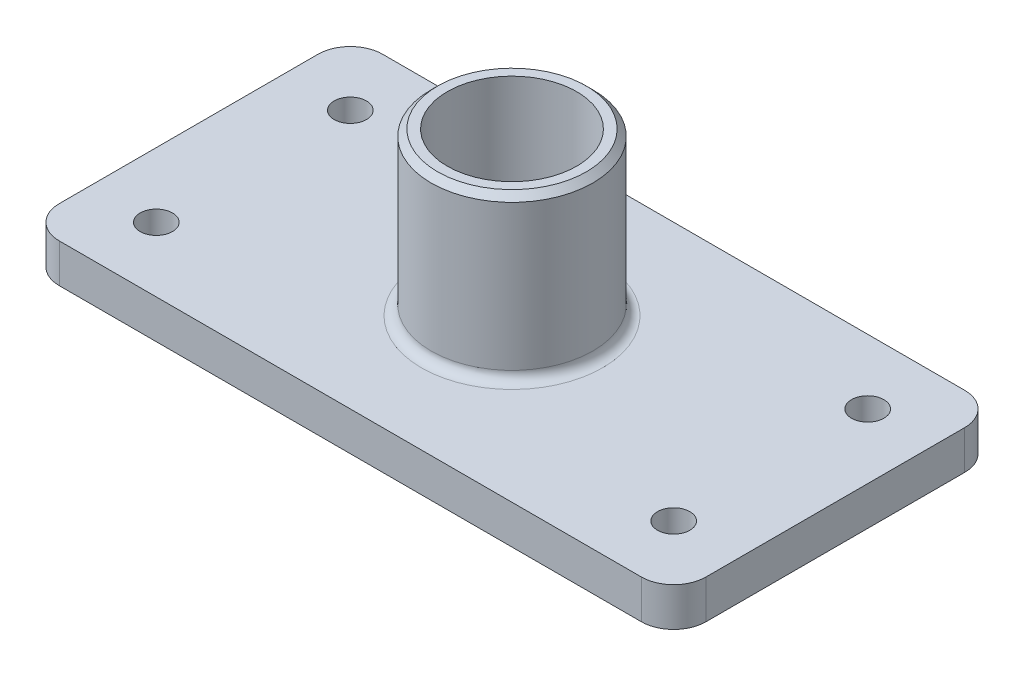
SolidWorks part; units mm, degrees
ref_plane "Front Plane" through (0, 0, 0) normal (0, 0, 1) x (1, 0, 0)
ref_plane "Top Plane" through (0, 0, 0) normal (0, 1, 0) x (1, 0, 0)
ref_plane "Right Plane" through (0, 0, 0) normal (1, 0, 0) x (0, 0, -1)
sketch "Sketch1" plane through (0, 0, 0) normal (0, 1, 0) x (1, 0, 0)
  line L1 (-90, -50) -> (90, -50)
  line L2 (-100, -40) -> (-100, 40)
  line L3 (-90, 50) -> (90, 50)
  line L4 (100, -40) -> (100, 40)
  line L5 (-100, -50) -> (100, 50) construction
  line L6 (-100, 50) -> (100, -50) construction
  arc A0 (90, -50) -> (100, -40) centre (90, -40) ccw
  arc A1 (90, 50) -> (100, 40) centre (90, 40) cw
  arc A2 (-100, 40) -> (-90, 50) centre (-90, 40) cw
  arc A3 (-90, -50) -> (-100, -40) centre (-90, -40) cw
  circle A4 centre (-80, -30) radius 5
  circle A5 centre (-80, 30) radius 5
  circle A6 centre (80, 30) radius 5
  circle A7 centre (80, -30) radius 5
  point P0 (0, 0)
  dimension "D3" = 10
  dimension "D4" = 10
  dimension "D1" = 100
  dimension "D2" = 200
  dimension "D5" = 20
  dimension "D6" = 60
  dimension "D7" = 20
  dimension "D8" = 160
extrude "Boss-Extrude1" add sketch "Sketch1" along normal blind 12
sketch "Sketch2" plane through (0, 12, 0) normal (0, 1, 0) x (1, 0, 0)
  circle A0 centre (0, 0) radius 25
  dimension "D1" = 50
extrude "Boss-Extrude2" add sketch "Sketch2" along normal blind 50
sketch "Sketch3" plane through (0, 62, 0) normal (0, 1, 0) x (1, 0, 0)
  circle A0 centre (0, 0) radius 20
  dimension "D1" = 40
extrude "Cut-Extrude1" cut sketch "Sketch3" against normal through all
fillet "Fillet1" radius 3 1 edges at (0, 12, 25)
chamfer "Chamfer1" distance 2 angle 45 1 edges at (0, 62, 25)
